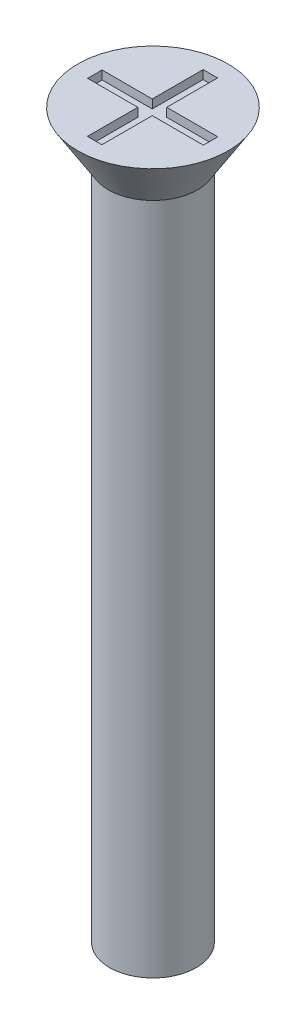
SolidWorks part; units mm, degrees
material "AISI 304"
ref_plane "Front" through (0, 0, 0) normal (0, 0, 1) x (1, 0, 0)
ref_plane "Top" through (0, 0, 0) normal (0, 1, 0) x (1, 0, 0)
ref_plane "Right" through (0, 0, 0) normal (1, 0, 0) x (0, 0, -1)
sketch "Sketch1" plane through (0, 0, 0) normal (0, 1, 0) x (1, 0, 0)
  circle A0 centre (0, 0) radius 1.5
  dimension "D1" = 3
extrude "Boss-Extrude1" add sketch "Sketch1" along normal blind 25
sketch "Sketch2" plane through (0, 25, 0) normal (0, 1, 0) x (1, 0, 0)
  circle A0 centre (0, 0) radius 2.6
  dimension "D1" = 5.2
extrude "Boss-Extrude2" add sketch "Sketch2" against normal blind 1.7 draft 32
sketch "Sketch3" plane through (0, 25, 0) normal (0, 1, 0) x (1, 0, 0)
  line L1 (-2, 0.2416) -> (2, 0.2416)
  line L2 (-2, 0.2416) -> (-2, -0.2584)
  line L3 (-2, -0.2584) -> (2, -0.2584)
  line L4 (2, 0.2416) -> (2, -0.2584)
  line L5 (-0.2653, 2) -> (0.2347, 2)
  line L6 (-0.2653, 2) -> (-0.2653, -2)
  line L7 (-0.2653, -2) -> (0.2347, -2)
  line L8 (0.2347, 2) -> (0.2347, -2)
  circle A0 centre (0, 0) radius 2.6 construction
  dimension "D1" = 0.5
  dimension "D2" = 0.5
  dimension "D3" = 4
  dimension "D4" = 4
  dimension "D5" = 2
  dimension "D6" = 2
extrude "Cut-Extrude1" cut sketch "Sketch3" against normal blind 0.3 contours L8 L5 L6 L1 | L8 L3 L6 L7 | L6 L1 L2 L3 | L1 L8 L3 L4 | L8 L1 L6 L3
